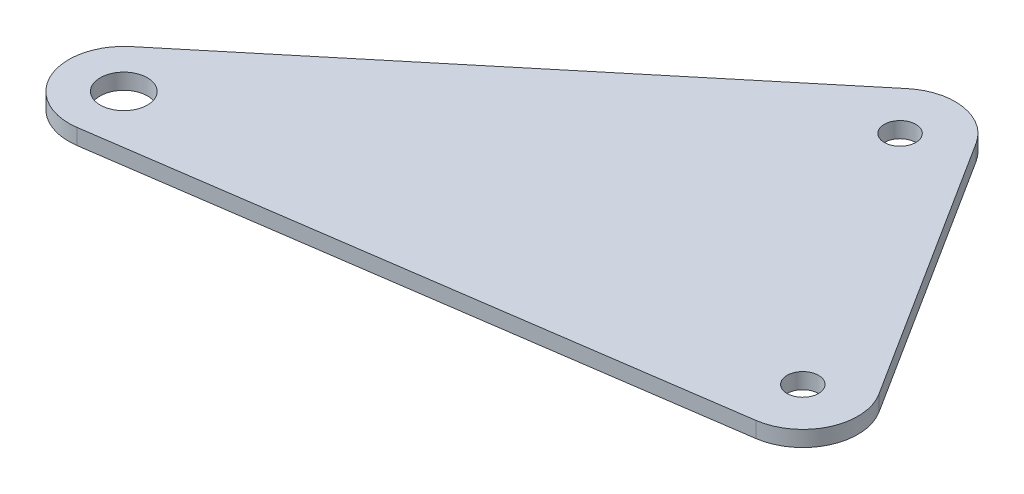
SolidWorks part; units mm, degrees
material "7075-O (SS)"
ref_plane "Płaszczyzna XY" through (0, 0, 0) normal (0, 0, 1) x (1, 0, 0)
ref_plane "Płaszczyzna XZ" through (0, 0, 0) normal (0, 1, 0) x (1, 0, 0)
ref_plane "Płaszczyzna YZ" through (0, 0, 0) normal (1, 0, 0) x (0, 0, -1)
sketch "Szkic1" plane through (0, 0, 0) normal (0, 1, 0) x (1, 0, 0)
  line L0 (1880.0779, -1039.0926) -> (1804.7482, -1049.977)
  line L1 (1884.9878, -1028.4147) -> (1863.5599, -994.6382)
  line L2 (1799.2811, -1037.6588) -> (1853.183, -992.9979)
  circle A0 centre (1803.7472, -1043.0489) radius 3
  circle A1 centre (1857.649, -998.3881) radius 2
  circle A2 centre (1879.0769, -1032.1645) radius 2
  arc A3 (1880.0779, -1039.0926) -> (1884.9878, -1028.4147) centre (1879.0769, -1032.1645) ccw
  arc A4 (1863.5599, -994.6382) -> (1853.183, -992.9979) centre (1857.649, -998.3881) ccw
  arc A5 (1799.2811, -1037.6588) -> (1804.7482, -1049.977) centre (1803.7472, -1043.0489) ccw
  dimension "D1" = 4
  dimension "D2" = 4
  dimension "D3" = 6
  dimension "D4" = 14
  dimension "D5" = 14
  dimension "D6" = 14
extrude "Dodanie-wyciągnięcie1" add sketch "Szkic1" along normal blind 2
